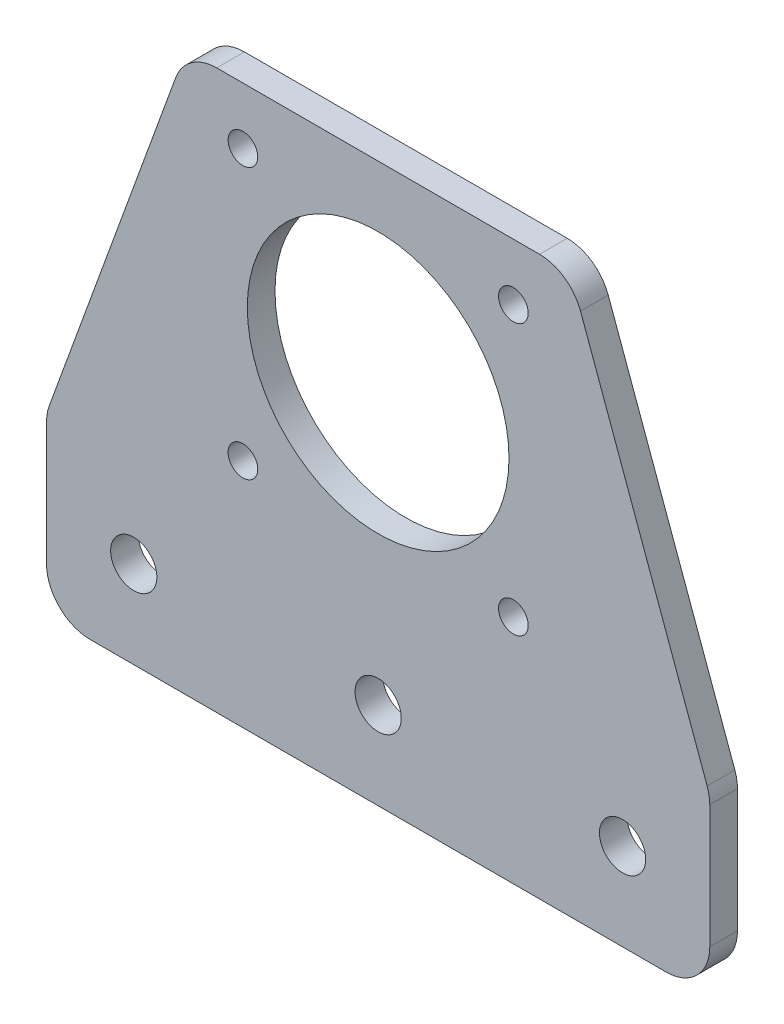
SolidWorks part; units mm, degrees
ref_plane "Front Plane" through (0, 0, 0) normal (0, 0, 1) x (1, 0, 0)
ref_plane "Top Plane" through (0, 0, 0) normal (0, 1, 0) x (1, 0, 0)
ref_plane "Right Plane" through (0, 0, 0) normal (1, 0, 0) x (0, 0, -1)
sketch "Sketch1" plane through (0, 0, 0) normal (0, 0, 1) x (1, 0, 0)
  line L8 (-22, 22) -> (22, 22)
  line L9 (-22, -22) -> (22, -22) construction
  line L10 (-22, -22) -> (-22, 22) construction
  line L11 (-22, 22) -> (22, 22) construction
  line L12 (22, -22) -> (22, 22) construction
  line L13 (-22, -22) -> (22, 22) construction
  line L14 (-22, 22) -> (22, -22) construction
  line L15 (22, 22) -> (38.0147, -22)
  line L16 (38.0147, -22) -> (38.0147, -42)
  line L17 (38.0147, -42) -> (-38.0147, -42)
  line L18 (-38.0147, -42) -> (-38.0147, -22)
  line L19 (-38.0147, -22) -> (-22, 22)
  line L20 (-38.0147, -22) -> (38.0147, -22) construction
  circle A0 centre (0, 0) radius 15
  dimension "D1" = 30
  dimension "D2" = 44
  dimension "D3" = 20
  dimension "D4" = 70
  dimension "D5" = 70
  dimension "D7" = 42
extrude "Boss-Extrude1" add sketch "Sketch1" along normal blind 3.175
sketch "Sketch2" plane through (0, 0, 3.175) normal (0, 0, 1) x (1, 0, 0)
  line L0 (-28.0147, -32) -> (28.0147, -32) construction
  line L1 (-38.0147, -22) -> (-38.0147, -42) construction
  line L3 (-15.5, -15.5) -> (15.5, -15.5) construction
  line L7 (-15.5, -15.5) -> (-15.5, 15.5) construction
  line L9 (-15.5, 15.5) -> (15.5, 15.5) construction
  line L10 (15.5, -15.5) -> (15.5, 15.5) construction
  line L11 (-15.5, -15.5) -> (15.5, 15.5) construction
  line L12 (-15.5, 15.5) -> (15.5, -15.5) construction
  line L13 (0, -42) -> (0, -32) construction
  line L14 (-38.0147, -42) -> (38.0147, -42) construction
  circle A5 centre (15.5, 15.5) radius 1.7
  circle A6 centre (15.5, -15.5) radius 1.7
  circle A7 centre (-15.5, -15.5) radius 1.7
  circle A8 centre (-15.5, 15.5) radius 1.7
  circle A9 centre (0, -32) radius 2.65
  circle A10 centre (28.0147, -32) radius 2.65
  circle A11 centre (-28.0147, -32) radius 2.65
  point P0 (0, 0)
  dimension "D3" = 10
  dimension "D4" = 5.3
  dimension "D1" = 3.4
  dimension "D2" = 31
  dimension "D5" = 10
extrude "Cut-Extrude1" cut sketch "Sketch2" against normal through all
fillet "Fillet1" radius 5 6 edges at (38.0147, -22, 1.5875) (38.0147, -42, 1.5875) (-38.0147, -42, 1.5875) (-22, 22, 1.5875) (22, 22, 1.5875) (-38.0147, -22, 1.5875)
equation "\"D5@Sketch1\"=\"D4@Sketch1\""
